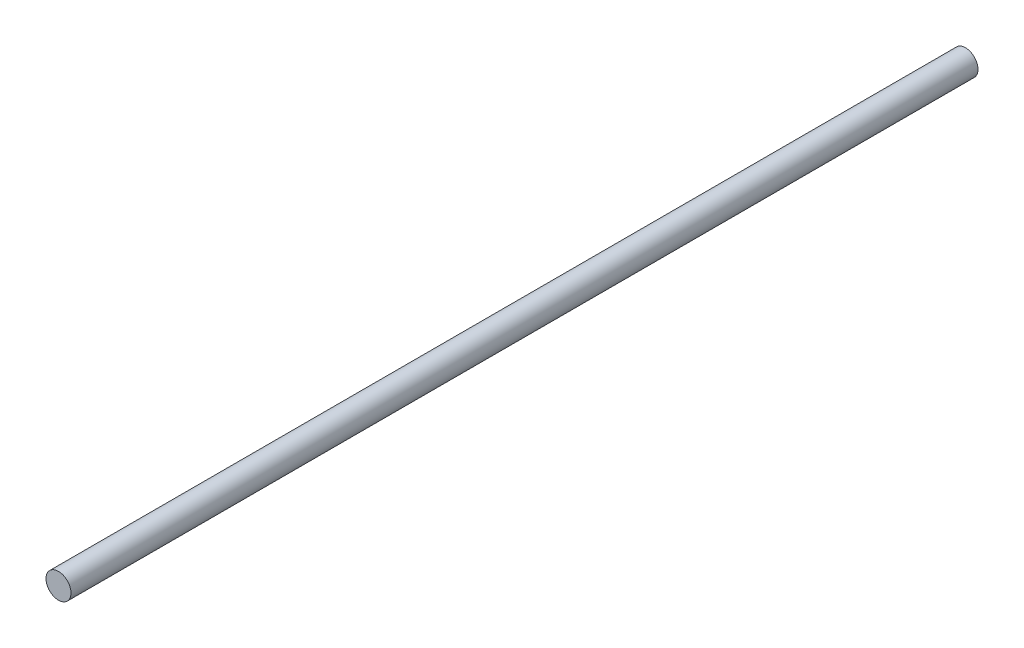
SolidWorks part; units mm, degrees
ref_plane "Front" through (0, 0, 0) normal (0, 0, 1) x (1, 0, 0)
ref_plane "Top" through (0, 0, 0) normal (0, 1, 0) x (1, 0, 0)
ref_plane "Right" through (0, 0, 0) normal (1, 0, 0) x (0, 0, -1)
sketch "Sketch1" plane through (0, 0, 0) normal (0, 0, 1) x (1, 0, 0)
  circle A1 centre (0, 0) radius 6.35
  dimension "D1" = 12.7
extrude "Boss-Extrude1" add sketch "Sketch1" along normal blind 460.502
